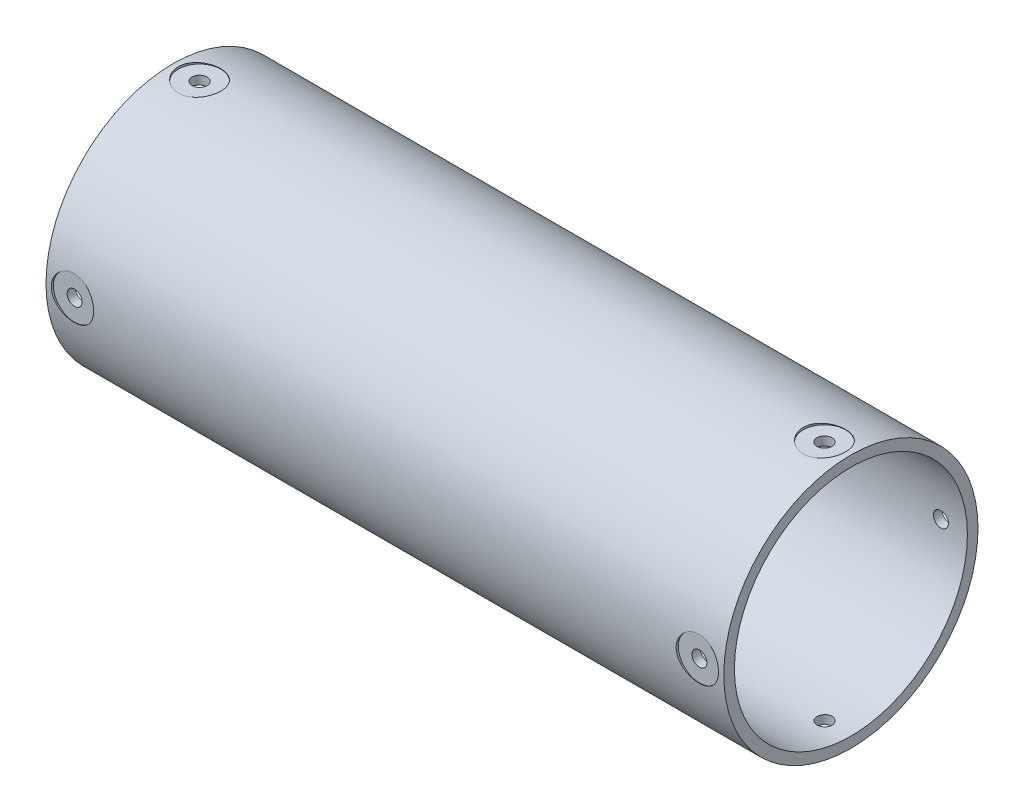
SolidWorks part; units mm, degrees
material "PVC Rigid"
ref_plane "Front" through (0, 0, 0) normal (0, 0, 1) x (1, 0, 0)
ref_plane "Top" through (0, 0, 0) normal (0, 1, 0) x (1, 0, 0)
ref_plane "Right" through (0, 0, 0) normal (1, 0, 0) x (0, 0, -1)
sketch "Sketch4" plane through (0, 0, 0) normal (1, 0, 0) x (0, 0, -1)
  circle A0 centre (0, 0) radius 38.1
  circle A1 centre (0, 0) radius 34.925
  circle A2 centre (0, 0) radius 12.7 construction
  point P5 (-38.1, 0)
  dimension "D1" = 76.2
  dimension "D2" = 3.175
  dimension "D3" = 25.4
sketch "Sketch5" plane through (0, 0, 0) normal (1, 0, 0) x (0, 0, -1)
  circle A0 centre (0, 0) radius 38.1 construction
  circle A1 centre (0, 0) radius 34.925 construction
  circle A2 centre (0, 0) radius 38.1
  circle A3 centre (0, 0) radius 34.925
extrude "Boss-Extrude3" add sketch "Sketch5" along normal mid plane 203.2
sketch "Sketch6" plane through (0, 0, 0) normal (0, 0, 1) x (1, 0, 0)
  line L0 (101.6, 0) -> (93.6625, 0) construction
  line L1 (101.6, -38.1) -> (101.6, 38.1) construction
  line L3 (97.6312, -3.9688) -> (89.6937, -3.9688)
  line L4 (97.6312, -3.9688) -> (97.6312, 3.9688)
  line L5 (97.6312, 3.9688) -> (89.6937, 3.9687)
  line L6 (89.6937, -3.9688) -> (89.6937, 3.9687)
  line L7 (97.6312, -3.9688) -> (89.6937, 3.9687) construction
  line L8 (97.6312, 3.9688) -> (89.6937, -3.9688) construction
  circle A0 centre (93.6625, 0) radius 1.5875
  dimension "D3" = 3.175
  dimension "D1" = 7.9375
  dimension "D2" = 7.9375
hole_wizard " Clearance Hole0" positions "3DSketch3" profile "Sketch8" hole size "#8" standard "ANSI Inch"
sketch3d "3DSketch3"
  point P0 (93.6625, 0, 38.1)
sketch "Sketch8" plane through (93.6625, 0, 38.1) normal (1, 0, 0) x (0, -1, 0)
  line L0 (0, 0) -> (0, 3.175)
  line L1 (0, 3.175) -> (2.2479, 3.175)
  line L2 (2.2479, 3.175) -> (2.2479, 0)
  line L5 (2.2479, 0) -> (0, 0)
  line L11 (0, -6.35) -> (0, 107.95) construction
  dimension "Thru Hole Dia." = 4.4958
  dimension "Thru Hole Depth" = 3.175
ref_plane "Plane1" through (0, 0, 38.1) normal (0, 0, 1) x (1, 0, 0)
sketch "Sketch10" plane through (0, 0, 38.1) normal (0, 0, 1) x (1, 0, 0)
  circle A0 centre (93.6625, 0) radius 6.35
  dimension "D1" = 12.7
extrude "Cut-Extrude2" cut sketch "Sketch10" against normal blind 0.635
pattern_circular "CirPattern1" count 4 over 360 about axis through (0, 0, 0) along (1, 0, 0) of " Clearance Hole0", "Cut-Extrude2"
mirror "Mirror1" about plane through (0, 0, 0) normal (1, 0, 0) of "CirPattern1", " Clearance Hole0", "Cut-Extrude2"
equation "\"motor_cap_nut\"=0.3125"
equation "\"D1@Sketch6\"=\"motor_cap_nut\""
equation "\"motor_cap_screw\"=0.125"
equation "\"D3@Sketch6\"=\"motor_cap_screw\""
equation "\"tol\"= 0.1mm"
